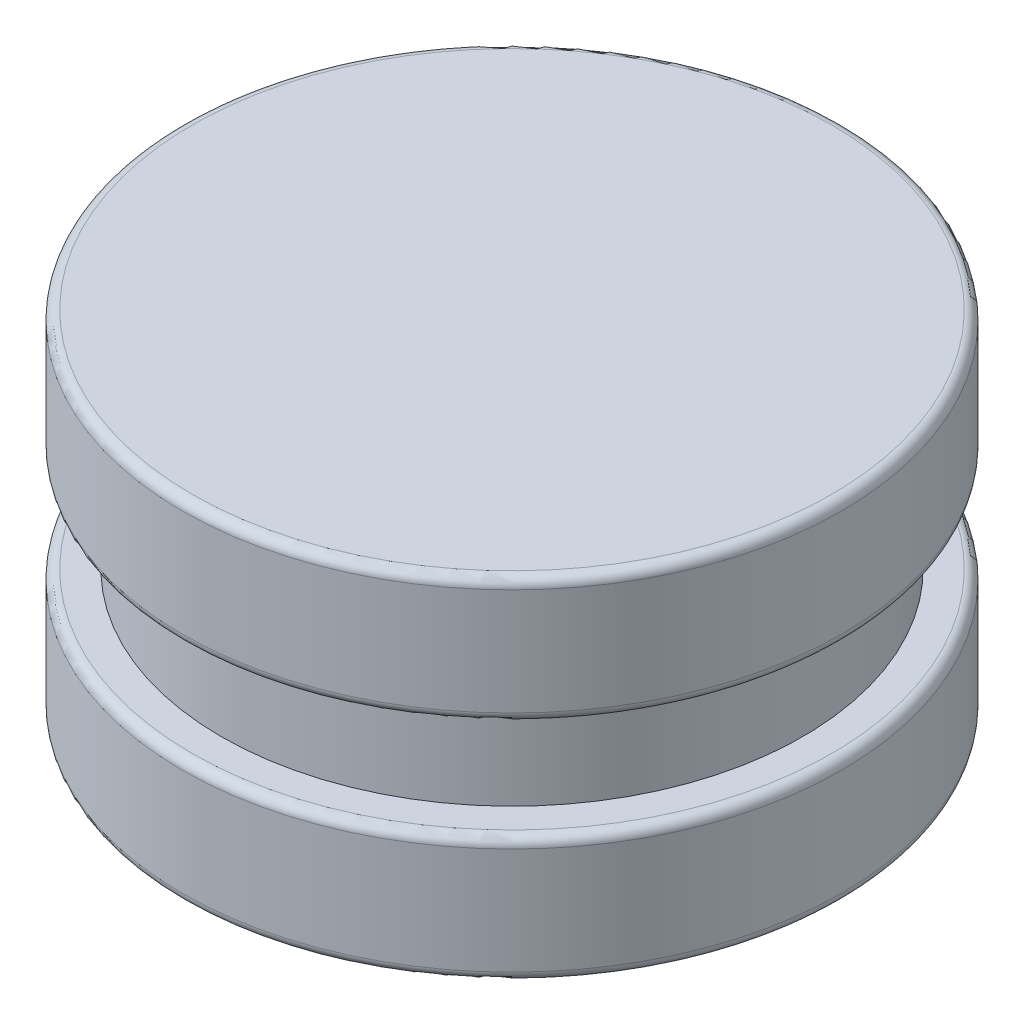
SolidWorks part; units mm, degrees
material "7075-T6 (SN)"
ref_plane "Top" through (0, 0, 0) normal (0, 0, 1) x (1, 0, 0)
ref_plane "Right" through (0, 0, 0) normal (0, 1, 0) x (1, 0, 0)
ref_plane "Front" through (0, 0, 0) normal (1, 0, 0) x (0, 0, -1)
sketch "Sketch1" plane through (0, 0, 0) normal (0, 1, 0) x (1, 0, 0)
  circle A0 centre (0, 0) radius 34.0004
  dimension "D1" = 68.0009
extrude "Boss-Extrude1" add sketch "Sketch1" along normal blind 13
fillet "Fillet1" radius 1 2 edges at (0, 13, 34.0004) (0, 0, 34.0004)
pattern_linear "LPattern1" count 2 spacing 23.16 along (0, 1, 0) of "Boss-Extrude1"
sketch "Sketch2" plane through (0, 13, 0) normal (0, 1, 0) x (1, 0, 0)
  circle A0 centre (0, 0) radius 30
  dimension "D1" = 60
extrude "Boss-Extrude2" add sketch "Sketch2" along normal up to next (23.16 mm away)
